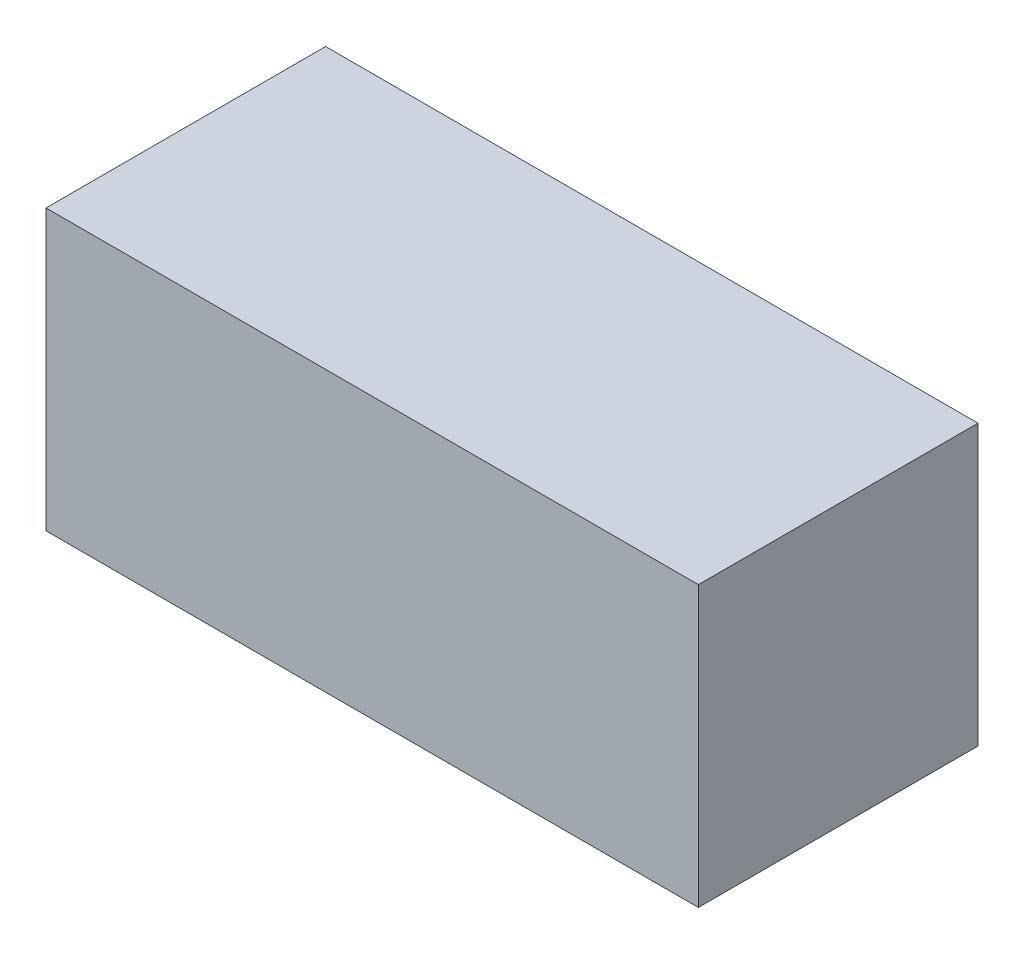
SolidWorks part; units mm, degrees
ref_plane "Front Plane" through (0, 0, 0) normal (0, 0, 1) x (1, 0, 0)
ref_plane "Top Plane" through (0, 0, 0) normal (0, 1, 0) x (1, 0, 0)
ref_plane "Right Plane" through (0, 0, 0) normal (1, 0, 0) x (0, 0, -1)
sketch "Sketch1" plane through (0, 0, 0) normal (0, 1, 0) x (1, 0, 0)
  line L1 (-44.45, -19.05) -> (44.45, -19.05)
  line L2 (-44.45, -19.05) -> (-44.45, 19.05)
  line L3 (-44.45, 19.05) -> (44.45, 19.05)
  line L4 (44.45, -19.05) -> (44.45, 19.05)
  line L5 (-44.45, -19.05) -> (44.45, 19.05) construction
  line L6 (-44.45, 19.05) -> (44.45, -19.05) construction
  point P0 (0, 0)
  dimension "D1" = 38.1
  dimension "D2" = 88.9
extrude "Boss-Extrude1" add sketch "Sketch1" along normal blind 38.1
